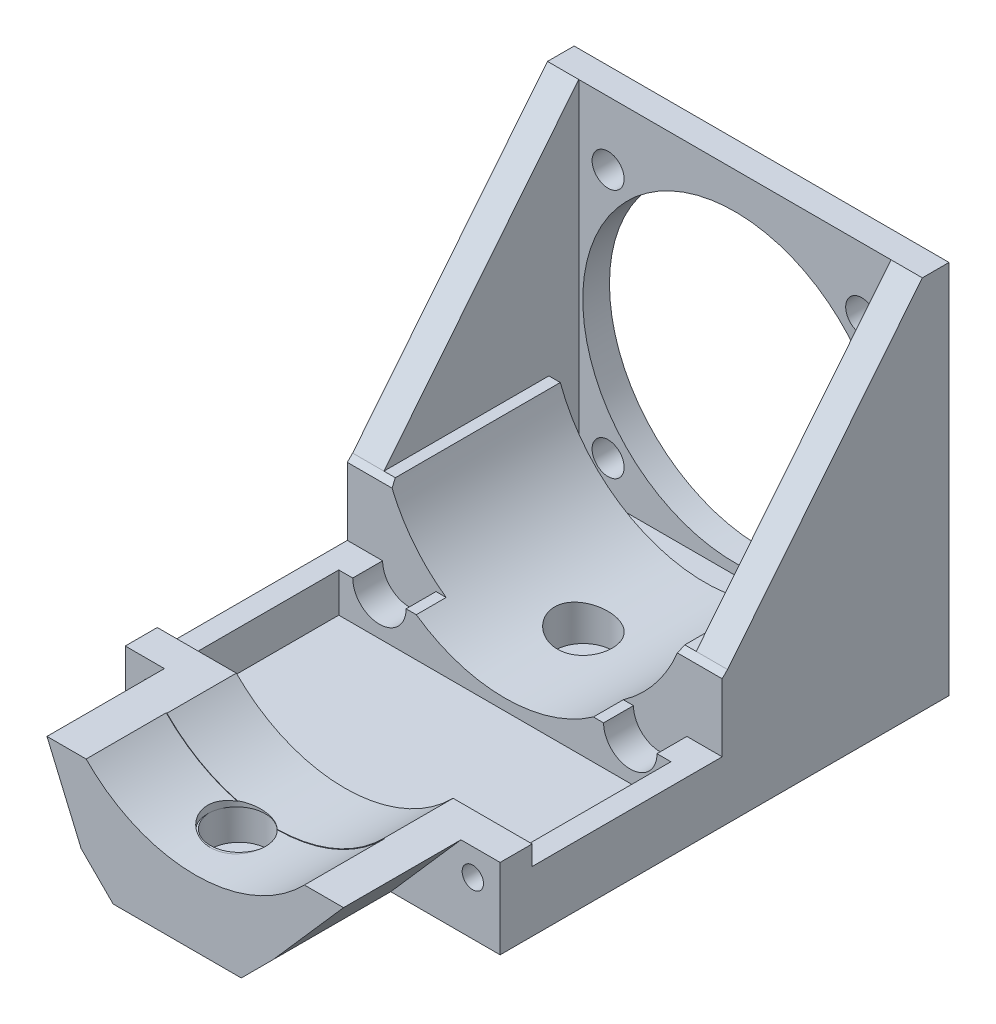
SolidWorks part; units mm, degrees
ref_plane "Ebene vorne" through (0, 0, 0) normal (0, 0, 1) x (1, 0, 0)
ref_plane "Ebene oben" through (0, 0, 0) normal (0, 1, 0) x (1, 0, 0)
ref_plane "Ebene rechts" through (0, 0, 0) normal (1, 0, 0) x (0, 0, -1)
sketch "Skizze1" plane through (0, 0, 0) normal (0, 0, 1) x (1, 0, 0)
  line L0 (27.1148, -10) -> (35.1148, -10)
  line L1 (-35.1148, -10) -> (-35.1148, -35)
  line L2 (-35.1148, -35) -> (35.1148, -35)
  line L3 (35.1148, -35) -> (35.1148, -10)
  line L5 (-35.1148, -10) -> (-27.1148, -10)
  arc A0 (-27.1148, -10) -> (27.1148, -10) centre (0, 0) ccw
  dimension "D1" = 28.9
  dimension "D4" = 35
  dimension "D2" = 8
  dimension "D3" = 8
  dimension "D5" = 25
extrude "Aufsatz-Linear austragen1" add sketch "Skizze1" along normal blind 43.1
sketch "Skizze2" plane through (0, 0, 0) normal (0, 0, -1) x (-1, 0, 0)
  line L0 (-23.5, -23.6637) -> (23.5, -23.6637)
  circle A0 centre (0, 0) radius 33.35
  circle A1 centre (-23.5, -23.6637) radius 2.55
  circle A2 centre (23.5, -23.6637) radius 2.55
  dimension "D1" = 66.7
  dimension "D3" = 5.1
  dimension "D4" = 5.1
  dimension "D2" = 47
extrude "Aufsatz-Linear austragen2" add sketch "Skizze2" along normal blind 5 draft 10 contours A2 | A1
sketch "Skizze3" plane through (0, 0, 43.1) normal (0, 0, 1) x (1, 0, 0)
  line L0 (28.5, -23.6637) -> (28.5, -7.7053)
  line L1 (28.5, -7.7053) -> (-28.5, -7.7053)
  line L2 (-28.5, -7.7053) -> (-28.5, -23.6637)
  line L3 (-18.5, -23.6637) -> (-18.5, -22.2027)
  line L4 (-18.5, -22.2027) -> (18.5, -22.2027)
  line L5 (18.5, -22.2027) -> (18.5, -23.6637)
  arc A0 (-28.5, -23.6637) -> (-18.5, -23.6637) centre (-23.5, -23.6637) ccw
  arc A1 (18.5, -23.6637) -> (28.5, -23.6637) centre (23.5, -23.6637) ccw
  arc A2 (-27.1148, -10) -> (27.1148, -10) centre (0, 0) ccw construction
  dimension "D2" = 10
  dimension "D3" = 10
  dimension "D1" = 47
extrude "Schnitt-Linear austragen1" cut sketch "Skizze3" against normal blind 5.6
chamfer "Fase1" distance 1 angle 45 2 edges at (27.8074, -10, 37.5) (-27.8074, -10, 37.5)
sketch "Skizze4" plane through (-28.5, 0, 0) normal (1, 0, 0) x (0, 0, -1)
  line L0 (-36.5, -10) -> (-37.5, -11)
  line L1 (-37.5, -11) -> (-37.5, -23.6637)
  line L2 (-37.5, -23.6637) -> (-43.1, -23.6637)
  line L3 (-43.1, -23.6637) -> (-43.1, -10)
  line L4 (-43.1, -10) -> (-36.5, -10)
extrude "Schnitt-Linear austragen2" cut sketch "Skizze4" against normal through all and the other way through all
sketch "Skizze5" plane through (0, 0, 43.1) normal (0, 0, 1) x (1, 0, 0)
  line L0 (-35.1148, -35) -> (-35.1148, -23.6637)
  line L1 (-35.1148, -23.6637) -> (-31.1148, -23.6637)
  line L2 (-35.1148, -23.6637) -> (-28.5, -23.6637) construction
  line L3 (-31.1148, -23.6637) -> (-31.1148, -31)
  line L4 (-31.1148, -31) -> (31.1148, -31)
  line L5 (31.1148, -31) -> (31.1148, -23.6637)
  line L6 (28.5, -23.6637) -> (35.1148, -23.6637) construction
  line L7 (31.1148, -23.6637) -> (35.1148, -23.6637)
  line L8 (35.1148, -23.6637) -> (35.1148, -35)
  line L9 (35.1148, -35) -> (-35.1148, -35)
  dimension "D1" = 4
  dimension "D2" = 4
  dimension "D3" = 4
extrude "Aufsatz-Linear austragen3" add sketch "Skizze5" along normal blind 30
sketch "Skizze6" plane through (0, 0, 73.1) normal (0, 0, 1) x (1, 0, 0)
  line L0 (35.1148, -35) -> (-35.1148, -35)
  line L1 (-35.1148, -35) -> (-35.1148, -20)
  line L2 (-35.1148, -20) -> (-20.3039, -20)
  line L3 (35.1148, -35) -> (35.1148, -20)
  line L4 (35.1148, -20) -> (20.3039, -20)
  arc A0 (-20.3039, -20) -> (20.3039, -20) centre (0, 0) ccw
  dimension "D1" = 57
  dimension "D2" = 15
  dimension "D3" = 15
extrude "Aufsatz-Linear austragen4" add sketch "Skizze6" along normal blind 13
sketch "Skizze7" plane through (0, 0, 86.1) normal (0, 0, 1) x (1, 0, 0)
  line L0 (35.1148, -35) -> (-35.1148, -35)
  line L1 (-35.1148, -35) -> (-35.1148, -20)
  line L2 (-35.1148, -20) -> (-35.1148, -35) construction
  line L3 (-35.1148, -20) -> (-20.4441, -20)
  line L4 (35.1148, -35) -> (35.1148, -20)
  line L5 (35.1148, -35) -> (35.1148, -20) construction
  line L6 (35.1148, -20) -> (20.4441, -20)
  arc A0 (-20.4441, -20) -> (20.4441, -20) centre (0, 0) ccw
  dimension "D1" = 57.2
  dimension "D2" = 15
  dimension "D3" = 15
extrude "Aufsatz-Linear austragen5" add sketch "Skizze7" along normal blind 15
ref_plane "Ebene1" through (0, -28.9, 0) normal (0, 1, 0) x (1, 0, 0)
sketch "Skizze24" plane through (0, 0, 0) normal (0, 0, -1) x (-1, 0, 0)
  line L0 (-8.62, -41) -> (-14.62, -35)
  line L2 (15.38, -41) -> (-8.62, -41)
  line L3 (15.38, -41) -> (21.38, -35)
  line L4 (0, -35) -> (0, -56.7382) construction
  line L7 (35.1148, -35) -> (-35.1148, -35) construction
  line L11 (21.38, -35) -> (-14.62, -35)
  dimension "D1" = 8.62
  dimension "D2" = 15.38
  dimension "D3" = 6
  dimension "D4" = 135
extrude "Aufsatz-Linear austragen6" add sketch "Skizze24" against normal up to surface (101.1 mm away) up to face at (0, -26.4333, 101.1)
hole_wizard "Ø1.0 (1) Durchmesser Bohrung1" positions "Skizze29" profile "Skizze28" hole size "Ø1.0" standard "ANSI Metrisch"
sketch "Skizze29" plane through (0, -41, 0) normal (0, -1, 0) x (-1, 0, 0)
  line L0 (27.1148, 0) -> (-27.1148, 0) construction
  line L1 (-8.62, 0) -> (15.38, 0) construction
  point P0 (3.38, -25)
  point P6 (3.38, 0)
  dimension "D1" = 25
  dimension "D2" = 0
sketch "Skizze28" plane through (-3.38, -41, 25) normal (1, 0, 0) x (0, 0, -1)
  line L0 (0, 0) -> (0, 25.3004)
  line L1 (0, 25.3004) -> (0.5, 25)
  line L2 (0.5, 25) -> (0.5, 0)
  line L5 (0.5, 0) -> (0, 0)
  line L10 (0, 25.3004) -> (-0.5, 25) construction
  line L11 (0, -6.35) -> (0, 107.95) construction
  dimension "Bohrerdurchmesser" = 1
  dimension "Bohrungstiefe" = 25
  dimension "Spitzenwinkel" = 118
hole_wizard "Stirnsenkung für M5 Zylinderschraube mit Innensechskant7" positions "Skizze31" profile "Skizze32" counterbore size "M5" standard "ANSI Metrisch"
sketch "Skizze31" plane through (0, -28.9, 0) normal (0, 1, 0) x (1, 0, 0)
  point P0 (-3.38, -25)
sketch "Skizze32" plane through (-3.38, -28.9, 25) normal (1, 0, 0) x (0, 0, -1)
  line L0 (0, 0) -> (0, 26.6524)
  line L1 (0, 26.6524) -> (2.75, 25)
  line L2 (2.75, 25) -> (2.75, 7)
  line L3 (2.75, 7) -> (5.4, 7)
  line L4 (5.4, 7) -> (5.4, 0)
  line L5 (5.4, 0) -> (0, 0)
  line L10 (0, 26.6524) -> (-2.75, 25) construction
  line L11 (0, -6.35) -> (0, 107.95) construction
  dimension "Bohrerdurchmesser" = 5.5
  dimension "Bohrungstiefe" = 25
  dimension "Senkdurchmesser2" = 10.8
  dimension "Senktiefe2" = 7
  dimension "Spitzenwinkel" = 118
hole_wizard "Ø1.0 (1) Durchmesser Bohrung2" positions "Skizze36" profile "Skizze35" hole size "Ø1.0" standard "ANSI Metrisch"
sketch "Skizze36" plane through (0, -41, 0) normal (0, -1, 0) x (-1, 0, 0)
  line L1 (27.1148, 0) -> (-27.1148, 0) construction
  line L2 (-8.62, 0) -> (15.38, 0) construction
  point P0 (3.38, -90)
  point P5 (3.38, 0)
  dimension "D1" = 90
  dimension "D2" = 0
sketch "Skizze35" plane through (-3.38, -41, 90) normal (1, 0, 0) x (0, 0, -1)
  line L0 (0, 0) -> (0, 25.3004)
  line L1 (0, 25.3004) -> (0.5, 25)
  line L2 (0.5, 25) -> (0.5, 0)
  line L5 (0.5, 0) -> (0, 0)
  line L10 (0, 25.3004) -> (-0.5, 25) construction
  line L11 (0, -6.35) -> (0, 107.95) construction
  dimension "Bohrerdurchmesser" = 1
  dimension "Bohrungstiefe" = 25
  dimension "Spitzenwinkel" = 118
ref_plane "Ebene2" through (0, -28.6, 0) normal (0, 1, 0) x (1, 0, 0)
hole_wizard "Stirnsenkung für M5 Zylinderschraube mit Innensechskant9" positions "Skizze40" profile "Skizze41" counterbore size "M5" standard "ANSI Metrisch"
sketch "Skizze40" plane through (0, -28.6, 0) normal (0, 1, 0) x (1, 0, 0)
  point P0 (-3.38, -90)
sketch "Skizze41" plane through (-3.38, -28.6, 90) normal (1, 0, 0) x (0, 0, -1)
  line L0 (0, 0) -> (0, 26.6524)
  line L1 (0, 26.6524) -> (2.75, 25)
  line L2 (2.75, 25) -> (2.75, 7)
  line L3 (2.75, 7) -> (5.4, 7)
  line L4 (5.4, 7) -> (5.4, 0)
  line L5 (5.4, 0) -> (0, 0)
  line L10 (0, 26.6524) -> (-2.75, 25) construction
  line L11 (0, -6.35) -> (0, 107.95) construction
  dimension "Bohrerdurchmesser" = 5.5
  dimension "Bohrungstiefe" = 25
  dimension "Senkdurchmesser2" = 10.8
  dimension "Senktiefe2" = 7
  dimension "Spitzenwinkel" = 118
sketch "Skizze45" plane through (0, 0, 0) normal (0, 0, -1) x (-1, 0, 0)
  line L0 (-35.1148, -35) -> (-14.62, -35)
  line L1 (21.38, -35) -> (35.1148, -35)
  line L2 (35.1148, -35) -> (35.1148, 35.2955)
  line L3 (-35.1148, 35.2955) -> (-35.1148, -35)
  line L5 (-35.1148, 35.2955) -> (35.1148, 35.2955)
  line L6 (-14.62, -35) -> (-8.62, -41)
  line L7 (-8.62, -41) -> (15.38, -41)
  line L8 (15.38, -41) -> (21.38, -35)
  line L10 (-23.5, -23.6637) -> (23.5, -23.6637)
  line L11 (-23.5, -23.6637) -> (-23.5, 23.7579)
  line L12 (23.5, -23.6637) -> (23.5, 23.7579)
  line L13 (-23.5, 23.7579) -> (23.5, 23.7579)
  circle A0 centre (0, 0) radius 28.9
  circle A1 centre (0, 0) radius 33.35
extrude "Aufsatz-Linear austragen7" add sketch "Skizze45" along normal blind 5 contours L5 L2 L1 L8 L7 L6 L0 L3
sketch "Skizze48" plane through (0, 0, 0) normal (0, 0, 1) x (1, 0, 0)
  circle A2 centre (0, 0) radius 28.5
extrude "Schnitt-Linear austragen4" cut sketch "Skizze48" against normal through all
sketch "Skizze49" plane through (0, -10, 0) normal (0, 1, 0) x (1, 0, 0)
  line L1 (29.2498, 0) -> (29.2498, -5.6)
  line L2 (29.2498, 0) -> (-29.2502, 0)
  line L3 (29.2498, -5.6) -> (-29.2502, -5.6)
  line L4 (-29.2502, -5.6) -> (-29.2502, 0)
  line L5 (35.1148, 0) -> (27.1148, 0) construction
  line L9 (35.1148, -36.5) -> (35.1148, 0) construction
  dimension "D1" = 58.5
  dimension "D2" = 5.865
  dimension "D3" = 5.6
extrude "Schnitt-Linear austragen8" cut sketch "Skizze49" against normal blind 20.5
sketch "Skizze50" plane through (0, 0, -5) normal (0, 0, -1) x (-1, 0, 0)
  line L1 (-23.7525, -23.396) -> (23.7525, -23.396)
  line L2 (-23.7525, -23.396) -> (-23.7525, 23.396)
  line L3 (-23.7525, 23.396) -> (23.7525, 23.396)
  line L4 (23.7525, -23.396) -> (23.7525, 23.396)
  line L5 (-23.7525, -23.396) -> (23.7525, 23.396) construction
  line L6 (-23.7525, 23.396) -> (23.7525, -23.396) construction
  point P0 (0, 0)
  dimension "D1" = 66.68
hole_wizard "Ø6.0 (6) Durchmesser Bohrung1" positions "Skizze52" profile "Skizze53" hole size "Ø6.0" standard "ANSI Metrisch" end condition up to next
sketch "Skizze52" plane through (0, 0, -5) normal (0, 0, -1) x (-1, 0, 0)
  point P0 (-23.7525, 23.396)
  point P3 (23.7525, 23.396)
  point P6 (23.7525, -23.396)
  point P9 (-23.7525, -23.396)
sketch "Skizze53" plane through (23.7525, 23.396, -5) normal (1, 0, 0) x (0, 1, 0)
  line L0 (0, 0) -> (0, 5)
  line L1 (0, 5) -> (3, 5)
  line L2 (3, 5) -> (3, 0)
  line L5 (3, 0) -> (0, 0)
  line L11 (0, -6.35) -> (0, 107.95) construction
  dimension "Bohrerdurchmesser" = 6
  dimension "Bohrungstiefe" = 5
sketch "Skizze54" plane through (-35.1148, 0, 0) normal (-1, 0, 0) x (0, 0, 1)
  line L0 (0, 35.2955) -> (36.5, -10)
  line L1 (36.5, -10) -> (0, -10)
  line L2 (0, -10) -> (0, 35.2955)
extrude "Aufsatz-Linear austragen8" add sketch "Skizze54" against normal up to surface (5.8645 mm away) contours L0 L1 L2 up to face at (-29.2502, -20.25, 2.8)
sketch "Skizze55" plane through (35.1148, 0, 0) normal (1, 0, 0) x (0, 0, -1)
  line L0 (0, 35.2955) -> (0, -10)
  line L1 (0, -10) -> (-36.5, -10)
  line L2 (-36.5, -10) -> (0, 35.2955)
extrude "Aufsatz-Linear austragen9" add sketch "Skizze55" against normal up to surface (5.865 mm away) up to face at (29.2498, -20.25, 2.8)
sketch "Skizze62" plane through (0, 0, 101.1) normal (0, 0, 1) x (1, 0, 0)
  line L0 (-35.1148, -20) -> (-27.7794, -20)
  line L1 (-20.4441, -20) -> (-35.1148, -20) construction
  line L2 (-27.7794, -20) -> (-21.38, -35)
  line L3 (-21.38, -35) -> (-35.1148, -35)
  line L4 (-35.1148, -35) -> (-35.1148, -20)
  line L5 (35.1148, -20) -> (27.7794, -20)
  line L6 (35.1148, -20) -> (20.4441, -20) construction
  line L7 (27.7794, -20) -> (14.62, -35)
  line L8 (14.62, -35) -> (35.1148, -35)
  line L9 (35.1148, -35) -> (35.1148, -20)
extrude "Schnitt-Linear austragen11" cut sketch "Skizze62" against normal blind 22
sketch "Skizze63" plane through (0, 0, 79.1) normal (0, 0, 1) x (1, 0, 0)
  line L0 (35.1148, -20) -> (27.7794, -20) construction
  line L1 (-27.7794, -20) -> (-35.1148, -20) construction
  circle A0 centre (-30, -25) radius 2.4191
  circle A1 centre (30, -25) radius 2.1363
  arc A2 (-16.5903, -23.6637) -> (16.5903, -23.6637) centre (0, 0) ccw construction
  arc A3 (-20.3039, -20) -> (20.3039, -20) centre (0, 0) ccw construction
  point P4 (0, -28.9)
  point P8 (0, -28.5)
  dimension "D1" = 30
  dimension "D2" = 30
  dimension "D3" = 5
  dimension "D4" = 5
hole_wizard "Ø4.0 (4) Durchmesser Bohrung2" positions "Skizze65" profile "Skizze64" hole size "Ø4.0" standard "ANSI Metrisch" end condition up to next
sketch "Skizze65" plane through (0, 0, 79.1) normal (0, 0, 1) x (1, 0, 0)
  point P0 (-30, -25)
  point P3 (30, -25)
sketch "Skizze64" plane through (-30, -25, 79.1) normal (1, 0, 0) x (0, -1, 0)
  line L0 (0, 0) -> (0, 6)
  line L1 (0, 6) -> (2, 6)
  line L2 (2, 6) -> (2, 0)
  line L5 (2, 0) -> (0, 0)
  line L11 (0, -6.35) -> (0, 107.95) construction
  dimension "Bohrerdurchmesser" = 4
  dimension "Bohrungstiefe" = 6
hole_wizard "Stirnsenkung für M5 Zylinderschraube mit Innensechskant13" positions "Skizze69" profile "Skizze68" counterbore size "M5" standard "ANSI Metrisch"
sketch "Skizze69" plane through (0, -28.6, 0) normal (0, 1, 0) x (1, 0, 0)
  circle A0 centre (-3.38, -90) radius 0.5 construction
  point P0 (-3.38, -25)
  point P3 (-3.38, -89.5)
sketch "Skizze68" plane through (-3.38, -28.6, 25) normal (1, 0, 0) x (0, 0, 1)
  line L0 (0, 0) -> (0, 26.5923)
  line L1 (0, 26.5923) -> (2.65, 25)
  line L2 (2.65, 25) -> (2.65, 6)
  line L3 (2.65, 6) -> (5.4, 6)
  line L4 (5.4, 6) -> (5.4, 0)
  line L5 (5.4, 0) -> (0, 0)
  line L10 (0, 26.5923) -> (-2.65, 25) construction
  line L11 (0, -6.35) -> (0, 107.95) construction
  dimension "Bohrerdurchmesser" = 5.3
  dimension "Bohrungstiefe" = 25
  dimension "Senkdurchmesser2" = 10.8
  dimension "Senktiefe2" = 6
  dimension "Spitzenwinkel" = 118
